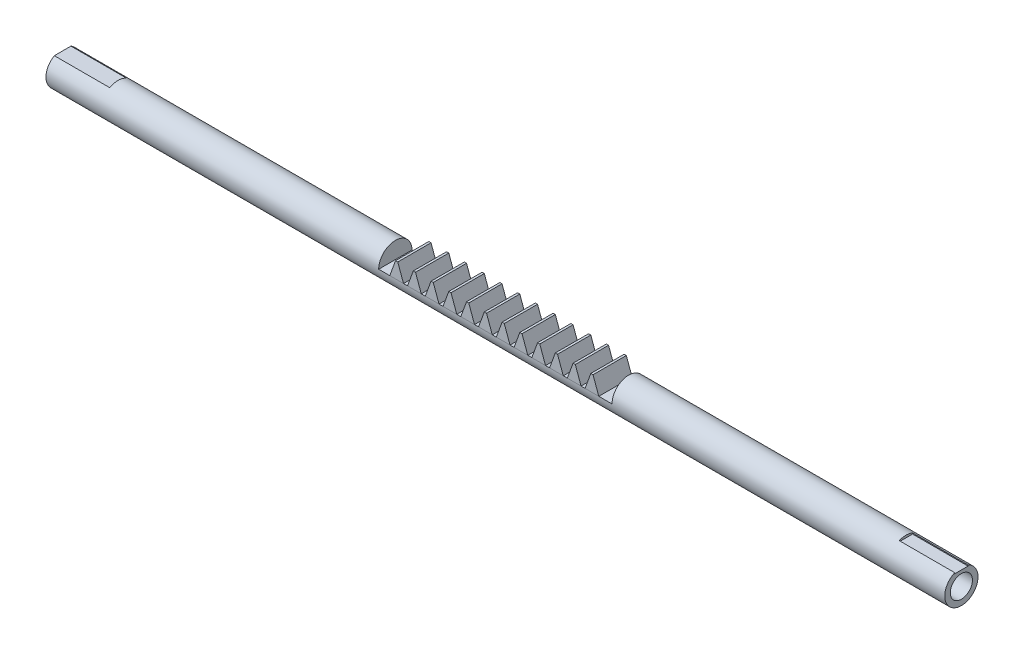
SolidWorks part; units mm, degrees
ref_plane "Front Plane" through (0, 0, 0) normal (0, 0, 1) x (1, 0, 0)
ref_plane "Top Plane" through (0, 0, 0) normal (0, 1, 0) x (1, 0, 0)
ref_plane "Right Plane" through (0, 0, 0) normal (1, 0, 0) x (0, 0, -1)
sketch "Sketch1" plane through (0, 0, 0) normal (1, 0, 0) x (0, 0, -1)
  circle A0 centre (0, 0) radius 0.375
  dimension "D1" = 0.75
extrude "Boss-Extrude1" add sketch "Sketch1" along normal blind 20.25
sketch "Sketch2" plane through (0, 0, 0) normal (0, 0, 1) x (1, 0, 0)
  line L0 (0, 0) -> (20.25, 0) construction
  line L1 (20.25, -0.375) -> (20.25, 0.375) construction
  dimension "D1" = 20.25
sketch "Sketch3" plane through (0, 0, 0) normal (1, 0, 0) x (0, 0, -1)
  circle A0 centre (0, 0) radius 0.25
  dimension "D1" = 0.5
extrude "Cut-Extrude1" cut sketch "Sketch3" along normal blind 6.5
ref_plane "Plane1" through (20.25, 0, 0) normal (1, 0, 0) x (0, 0, -1)
sketch "Sketch4" plane through (20.25, 0, 0) normal (1, 0, 0) x (0, 0, -1)
  circle A0 centre (0, 0) radius 0.25
  dimension "D1" = 0.5
extrude "Cut-Extrude2" cut sketch "Sketch4" against normal blind 6.5
sketch "Sketch5" plane through (20.25, 0, 0) normal (1, 0, 0) x (0, 0, -1)
  line L0 (0, 0) -> (0, 0.7438) construction
  line L2 (-0.15, 0.3219) -> (0.15, 0.3219)
  line L3 (-0.15, 0.3219) -> (-0.15, 0.4219)
  line L4 (-0.15, 0.4219) -> (0.15, 0.4219)
  line L5 (0.15, 0.3219) -> (0.15, 0.4219)
  line L6 (-0.15, 0.3219) -> (0.15, 0.4219) construction
  line L7 (-0.15, 0.4219) -> (0.15, 0.3219) construction
  point P3 (0, 0.3719)
  dimension "D1" = 0.05
  dimension "D2" = 0.3
extrude "Cut-Extrude3" cut sketch "Sketch5" against normal blind 1.25
sketch "Sketch6" plane through (0, 0, 0) normal (1, 0, 0) x (0, 0, -1)
  line L0 (0, 0) -> (0, 1.0852) construction
  line L2 (-0.25, 0.325) -> (0.25, 0.325)
  line L3 (-0.25, 0.325) -> (-0.25, 0.425)
  line L4 (-0.25, 0.425) -> (0.25, 0.425)
  line L5 (0.25, 0.325) -> (0.25, 0.425)
  line L6 (-0.25, 0.325) -> (0.25, 0.425) construction
  line L7 (-0.25, 0.425) -> (0.25, 0.325) construction
  circle A0 centre (0, 0) radius 0.375 construction
  point P3 (0, 0.375)
  dimension "D1" = 0.5
  dimension "D2" = 0.05
extrude "Cut-Extrude4" cut sketch "Sketch6" along normal blind 1.25
sketch "Sketch7" plane through (0, 0, 0) normal (0, 0, 1) x (1, 0, 0)
  line L0 (7.4961, 0) -> (12.7539, 0)
  line L1 (0, 0) -> (20.25, 0) construction
  line L2 (7.4961, 0) -> (7.4961, 0.4301)
  line L4 (7.4961, 0.4301) -> (12.7539, 0.4301)
  line L5 (12.7539, 0.4301) -> (12.7539, 0)
  point P5 (10.125, 0)
  dimension "D1" = 5.2577
extrude "Cut-Extrude5" cut sketch "Sketch7" against normal through all both and the other way through all
sketch "Sketch8" plane through (0, 0, 0) normal (0, 0, 1) x (1, 0, 0)
  line L0 (7.4961, 0) -> (7.7461, 0) construction
  line L1 (0, 0) -> (20.25, 0) construction
  line L2 (7.7461, 0) -> (7.7461, 0.375) construction
  line L3 (7.7461, 0) -> (7.8759, 0.3566)
  line L4 (7.8759, 0.3566) -> (7.9259, 0.3566)
  line L5 (7.9259, 0.3566) -> (8.0557, 0)
  line L6 (7.9259, 0.3566) -> (7.9259, 0) construction
  line L7 (7.7461, 0) -> (8.0557, 0)
  dimension "D1" = 0.25
  dimension "D2" = 20
  dimension "D3" = 0.05
  dimension "D4" = 20
extrude "Boss-Extrude2" add sketch "Sketch8" against normal through all and the other way through all
pattern_linear "LPattern1" count 12 spacing 0.4 along (1, 0, 0) of "Boss-Extrude2"
